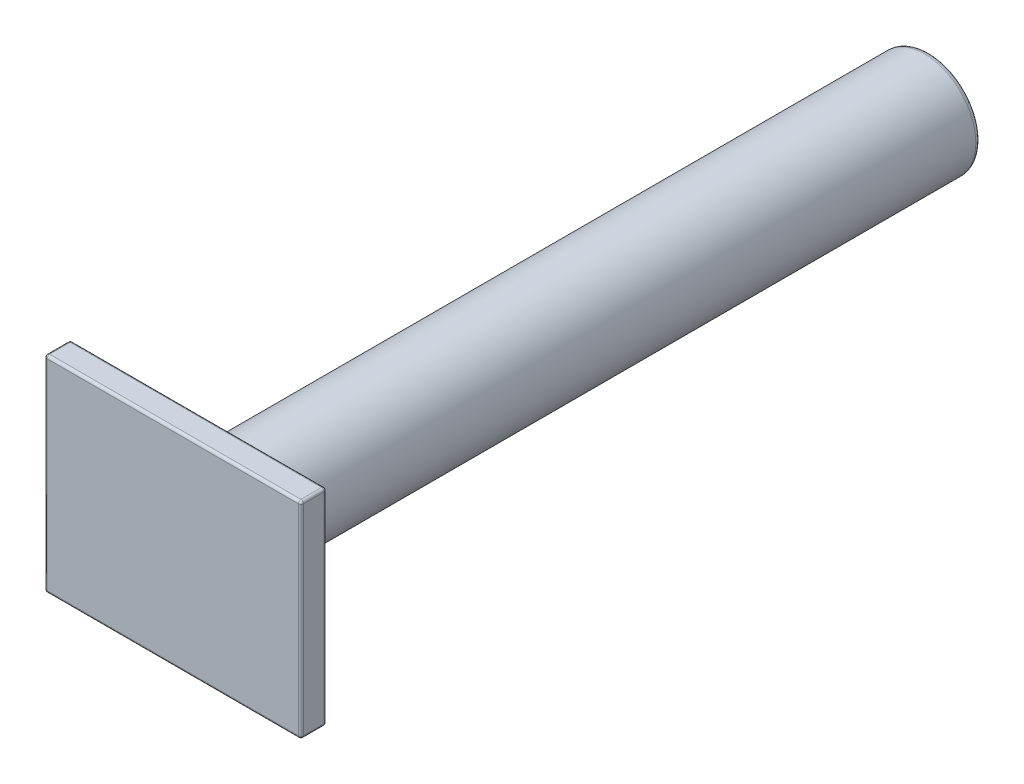
SolidWorks part; units mm, degrees
ref_plane "Front Plane" through (0, 0, 0) normal (0, 0, 1) x (1, 0, 0)
ref_plane "Top Plane" through (0, 0, 0) normal (0, 1, 0) x (1, 0, 0)
ref_plane "Right Plane" through (0, 0, 0) normal (1, 0, 0) x (0, 0, -1)
sketch "Sketch1" plane through (0, 0, 0) normal (0, 0, 1) x (1, 0, 0)
  circle A0 centre (0, 0) radius 20
  dimension "D1" = 40
extrude "Boss-Extrude1" add sketch "Sketch1" along normal blind 284
sketch "Sketch2" plane through (0, 0, 284) normal (0, 0, 1) x (1, 0, 0)
  line L1 (-49.8054, 40) -> (49.8054, 40)
  line L2 (-49.8054, 40) -> (-49.8054, -40)
  line L3 (-49.8054, -40) -> (49.8054, -40)
  line L4 (49.8054, 40) -> (49.8054, -40)
  line L5 (0, -40) -> (0, 40) construction
  line L6 (-49.8054, 0) -> (49.8054, 0) construction
  point P0 (0, 0)
  dimension "D1" = 80
extrude "Boss-Extrude2" add sketch "Sketch2" along normal blind 10
fillet "Fillet1" radius 2 1 edges at (20, 0, 0)
fillet "Fillet2" radius 1 12 edges at (49.8054, 40, 289) (-49.8054, 40, 289) (0, 40, 284) (0, -40, 294) (-49.8054, 0, 294) (0, 40, 294) (49.8054, 0, 294) (-49.8054, -40, 289) (49.8054, -40, 289) (0, -40, 284) (49.8054, 0, 284) (-49.8054, 0, 284)
